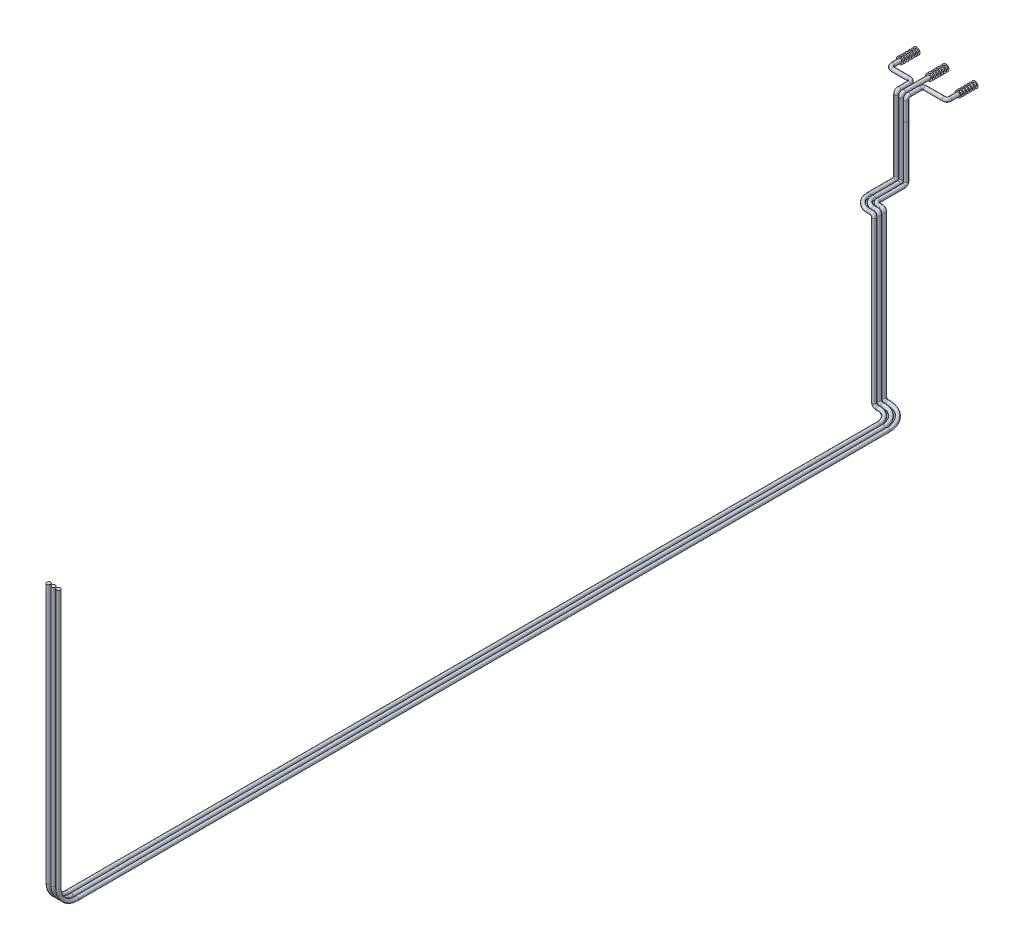
SolidWorks part; units mm, degrees
ref_plane "Alzado" through (0, 0, 0) normal (0, 0, 1) x (1, 0, 0)
ref_plane "Planta" through (0, 0, 0) normal (0, 1, 0) x (1, 0, 0)
ref_plane "Vista lateral" through (0, 0, 0) normal (1, 0, 0) x (0, 0, -1)
sketch "Croquis1" plane through (0, 0, 0) normal (0, 0, 1) x (1, 0, 0)
  line L0 (0, 0) -> (210, 0) construction
  line L1 (210, 0) -> (420, 0) construction
  circle A0 centre (0, 0) radius 13.7
  circle A1 centre (210, 0) radius 13.7
  circle A2 centre (210, 0) radius 13.7
  dimension "D1" = 27.4
  dimension "D3" = 27.4
  dimension "D2" = 210
  dimension "D4" = 210
sketch3d "Croquis3D1"
  line L0 (0, 0, 0) -> (0, 0, 170)
  line L1 (30, 0, 200) -> (145.0002, 0, 200)
  line L2 (175.0002, 0, 230) -> (175.0002, 0, 300)
  line L3 (175.0002, -20, 320) -> (175.0002, -156.8001, 320)
  arc A0 (0, 0, 170) -> (30, 0, 200) centre (30, 0, 170) ccw
  arc A1 (145.0002, 0, 200) -> (175.0002, 0, 230) centre (145.0002, 0, 230) ccw
  arc A2 (175.0002, 0, 300) -> (175.0002, -20, 320) centre (175.0002, -20, 300) ccw
  point P10 (0, 0, 200)
  point P11 (30, 30, 170)
  point P14 (175.0002, 0, 200)
  point P15 (145.0002, -30, 230)
  point P19 (175.0002, 0, 320)
  point P20 (195.0002, -20, 300)
  dimension "D1" = 30
  dimension "D2" = 20
  dimension "D3" = 175.0002
  dimension "D4" = 200
  dimension "D5" = 120
sweep "Barrer5" add path "Croquis3D1" circular profile diameter 27.4 parameters "D3"=27.4
sketch "Croquis14" plane through (0, 0, 0) normal (0, 0, 1) x (1, 0, 0)
  circle A0 centre (210, 0) radius 13.7
sketch3d "Croquis3D2"
  line L0 (210, 0, 0) -> (210, 0, 299.997)
  line L1 (210, -20, 319.997) -> (210, -153.4253, 319.997)
  arc A0 (210, 0, 299.997) -> (210, -20, 319.997) centre (210, -20, 299.997) ccw
  point P8 (210, 0, 319.997)
  point P9 (230, -20, 299.997)
  dimension "D1" = 20
  dimension "D2" = 319.997
sweep "Barrer6" add path "Croquis3D2" circular profile diameter 27.4 parameters "D3"=27.4
sketch "Croquis41" plane through (0, 0, 0) normal (0, 0, -1) x (-1, 0, 0)
  circle A0 centre (-420, 0) radius 13.7
  dimension "D1" = 27.4
sketch3d "Croquis3D3"
  line L0 (420, 0, 0) -> (420, 0, 180)
  line L1 (400, 0, 200) -> (264.998, 0, 200)
  line L2 (244.998, 0, 220) -> (244.998, 0, 300)
  line L3 (244.998, -20, 320) -> (244.998, -158.8149, 320)
  arc A0 (244.998, 0, 300) -> (244.998, -20, 320) centre (244.998, -20, 300) ccw
  arc A1 (420, 0, 180) -> (400, 0, 200) centre (400, 0, 180) ccw
  arc A2 (264.998, 0, 200) -> (244.998, 0, 220) centre (264.998, 0, 220) ccw
  point P8 (244.998, 0, 320)
  point P9 (264.998, -20, 300)
  point P12 (420, 0, 200)
  point P13 (400, -20, 180)
  point P16 (244.998, 0, 200)
  point P17 (264.998, 20, 220)
  dimension "D1" = 20
  dimension "D2" = 175.002
  dimension "D3" = 200
  dimension "D4" = 120
sweep "Barrer7" add profiles "Croquis41" path "Croquis3D3"
sketch "Croquis62" plane through (0, 0, 0) normal (0, 0, -1) x (-1, 0, 0)
  circle A0 centre (-420, 0) radius 22.8702
  circle A1 centre (-210, 0) radius 24.3657
  circle A2 centre (0, 0) radius 24.738
extrude "Saliente-Extruir1" add sketch "Croquis62" along normal blind 1
pattern_linear "MatrizL1" count 7 spacing 20 along (0, 0, 1) of "Saliente-Extruir1"
sketch "Croquis64" plane through (0, -158.8149, 0) normal (0, -1, 0) x (1, 0, 0)
  line L1 (71.8798, 336.7936) -> (310.9459, 336.7936)
  line L2 (71.8798, 336.7936) -> (71.8798, 303.5924)
  line L3 (71.8798, 303.5924) -> (310.9459, 303.5924)
  line L4 (310.9459, 336.7936) -> (310.9459, 303.5924)
  line L5 (71.8798, 336.7936) -> (310.9459, 303.5924) construction
  line L6 (71.8798, 303.5924) -> (310.9459, 336.7936) construction
  point P0 (191.4129, 320.193)
extrude "Cortar-Extruir1" cut sketch "Croquis64" against normal blind 5
sketch "Croquis65" plane through (0, -153.4253, 0) normal (0, -1, 0) x (1, 0, 0)
  circle A0 centre (175.0002, 320) radius 13.7
  circle A1 centre (210, 319.997) radius 13.7
  circle A2 centre (244.998, 320) radius 13.697
sketch3d "Croquis3D4"
  line L0 (175.0002, -153.4253, 320) -> (175.0002, -531.3553, 320)
  line L1 (175.0002, -551.3553, 340) -> (175.0002, -551.3553, 520)
  line L2 (275.0002, -551.3553, 620) -> (295.0002, -551.3553, 620)
  line L3 (315.0002, -571.3553, 620) -> (315.0002, -1730.3553, 620)
  line L4 (335.0002, -1750.3553, 620) -> (344.6398, -1750.3553, 620)
  line L5 (444.6398, -1750.3553, 720) -> (444.6398, -1750.3553, 6577.7185)
  line L6 (444.6398, -1620.3553, 6707.7185) -> (444.6398, 249.6447, 6707.7185)
  arc A0 (315.0002, -1730.3553, 620) -> (335.0002, -1750.3553, 620) centre (335.0002, -1730.3553, 620) ccw
  arc A1 (295.0002, -551.3553, 620) -> (315.0002, -571.3553, 620) centre (295.0002, -571.3553, 620) ccw
  arc A2 (175.0002, -531.3553, 320) -> (175.0002, -551.3553, 340) centre (175.0002, -531.3553, 340) ccw
  arc A3 (175.0002, -551.3553, 520) -> (275.0002, -551.3553, 620) centre (275.0002, -551.3553, 520) ccw
  arc A4 (344.6398, -1750.3553, 620) -> (444.6398, -1750.3553, 720) centre (344.6398, -1750.3553, 720) ccw
  arc A5 (444.6398, -1750.3553, 6577.7185) -> (444.6398, -1620.3553, 6707.7185) centre (444.6398, -1620.3553, 6577.7185) ccw
  point P9 (444.6398, -1750.3553, 620)
  point P10 (344.6398, -1850.3553, 720)
  point P13 (315.0002, -1750.3553, 620)
  point P14 (335.0002, -1730.3553, 640)
  point P17 (315.0002, -551.3553, 620)
  point P18 (295.0002, -571.3553, 600)
  point P21 (175.0002, -551.3553, 320)
  point P22 (155.0002, -531.3553, 340)
  point P26 (175.0002, -551.3553, 620)
  point P27 (275.0002, -451.3553, 520)
  point P31 (444.6398, -1750.3553, 6707.7185)
  point P32 (314.6398, -1620.3553, 6577.7185)
  dimension "D3" = 20
  dimension "D4" = 100
  dimension "D6" = 100
  dimension "D8" = 130
  dimension "D1" = 397.93
  dimension "D2" = 300
  dimension "D5" = 140
  dimension "D7" = 6087.7185
  dimension "D9" = 2000
  dimension "D10" = 129.6397
  dimension "D11" = 1199
sweep "Barrer10" add profiles "Croquis65" path "Croquis3D4"
